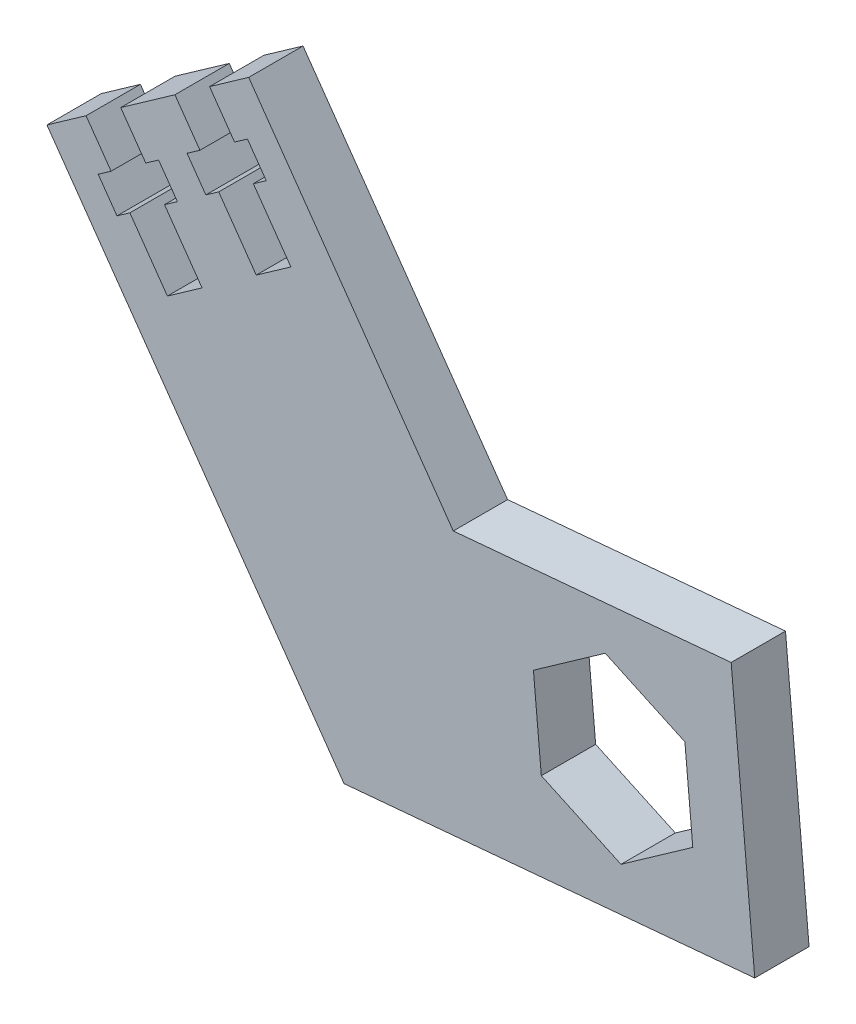
SolidWorks part; units mm, degrees
ref_plane "Front Plane" through (0, 0, 0) normal (0, 0, 1) x (1, 0, 0)
ref_plane "Top Plane" through (0, 0, 0) normal (0, 1, 0) x (1, 0, 0)
ref_plane "Right Plane" through (0, 0, 0) normal (1, 0, 0) x (0, 0, -1)
sketch "Sketch3" plane through (0, 0, 4.3766) normal (0, 0, 1) x (1, 0, 0)
  line L0 (-41.0959, 37.6696) -> (-13.7546, -1.1555)
  line L1 (3.6741, 16.602) -> (4.4, 8.5546)
  line L2 (4.4, 8.5546) -> (11.7321, 5.1595)
  line L3 (11.7321, 5.1595) -> (18.3383, 9.8118)
  line L4 (18.3383, 9.8118) -> (17.6125, 17.8591)
  line L5 (17.6125, 17.8591) -> (10.2804, 21.2542)
  line L6 (10.2804, 21.2542) -> (3.6741, 16.602)
  line L10 (-22.5285, 50.7451) -> (-26.1298, 48.209)
  line L11 (-31.8122, 44.2073) -> (-0.6964, 0.0223) construction
  line L12 (-34.3059, 42.4512) -> (-32.0028, 39.1808)
  line L13 (-15.5414, 12.4185) -> (-28.4152, 30.6996) construction
  line L14 (-26.8208, 31.8223) -> (-30.0095, 29.5768)
  line L15 (-30.2755, 36.728) -> (-29.09, 37.5628)
  line L16 (-29.09, 37.5628) -> (-30.8173, 40.0157)
  line L17 (-32.0028, 39.1808) -> (-30.8173, 40.0157)
  line L18 (-30.2755, 36.728) -> (-26.8208, 31.8223)
  line L19 (-33.4642, 34.4825) -> (-30.0095, 29.5768)
  line L20 (-35.1915, 36.9353) -> (-36.377, 36.1004)
  line L21 (-34.6497, 33.6476) -> (-36.377, 36.1004)
  line L22 (-33.4642, 34.4825) -> (-34.6497, 33.6476)
  line L23 (-37.4946, 40.2057) -> (-35.1915, 36.9353)
  line L24 (-29.3185, 45.9635) -> (-34.3059, 42.4512)
  line L25 (-37.4946, 40.2057) -> (-41.0959, 37.6696)
  line L26 (-13.7546, -1.1555) -> (24.0404, 2.2534)
  line L27 (24.0404, 2.2534) -> (21.8701, 26.3158)
  line L28 (21.8701, 26.3158) -> (-3.7008, 24.0094)
  line L29 (-26.1298, 48.209) -> (-23.8267, 44.9385)
  line L30 (-7.3653, 18.1762) -> (-20.2391, 36.4573) construction
  line L31 (-18.6448, 37.5801) -> (-21.8334, 35.3345)
  line L32 (-22.0994, 42.4857) -> (-20.9139, 43.3206)
  line L33 (-20.9139, 43.3206) -> (-22.6412, 45.7734)
  line L34 (-23.8267, 44.9385) -> (-22.6412, 45.7734)
  line L35 (-22.0994, 42.4857) -> (-18.6448, 37.5801)
  line L36 (-25.2881, 40.2402) -> (-21.8334, 35.3345)
  line L37 (-27.0154, 42.693) -> (-28.2009, 41.8581)
  line L38 (-26.4736, 39.4053) -> (-28.2009, 41.8581)
  line L39 (-25.2881, 40.2402) -> (-26.4736, 39.4053)
  line L40 (-29.3185, 45.9635) -> (-27.0154, 42.693)
  line L41 (-3.7008, 24.0094) -> (-22.5285, 50.7451)
  line L42 (22.9552, 14.2846) -> (-18.2085, 10.5719) construction
  circle A0 centre (11.0062, 13.2069) radius 6.9975 construction
  point P37 (-7.3653, 18.1762)
  point P42 (-15.5414, 12.4185)
  dimension "D1" = 8.08
  dimension "D2" = 50
  dimension "D3" = 120
  dimension "D4" = 4
  dimension "D5" = 3.9
  dimension "D6" = 4
  dimension "D7" = 6
  dimension "D8" = 3
  dimension "D9" = 1.45
  dimension "D10" = 3.9
  dimension "D11" = 4
  dimension "D12" = 6
  dimension "D13" = 3
  dimension "D14" = 1.45
  dimension "D15" = 5
  dimension "D16" = 5
extrude "Boss-Extrude1" add sketch "Sketch3" against normal blind 5
